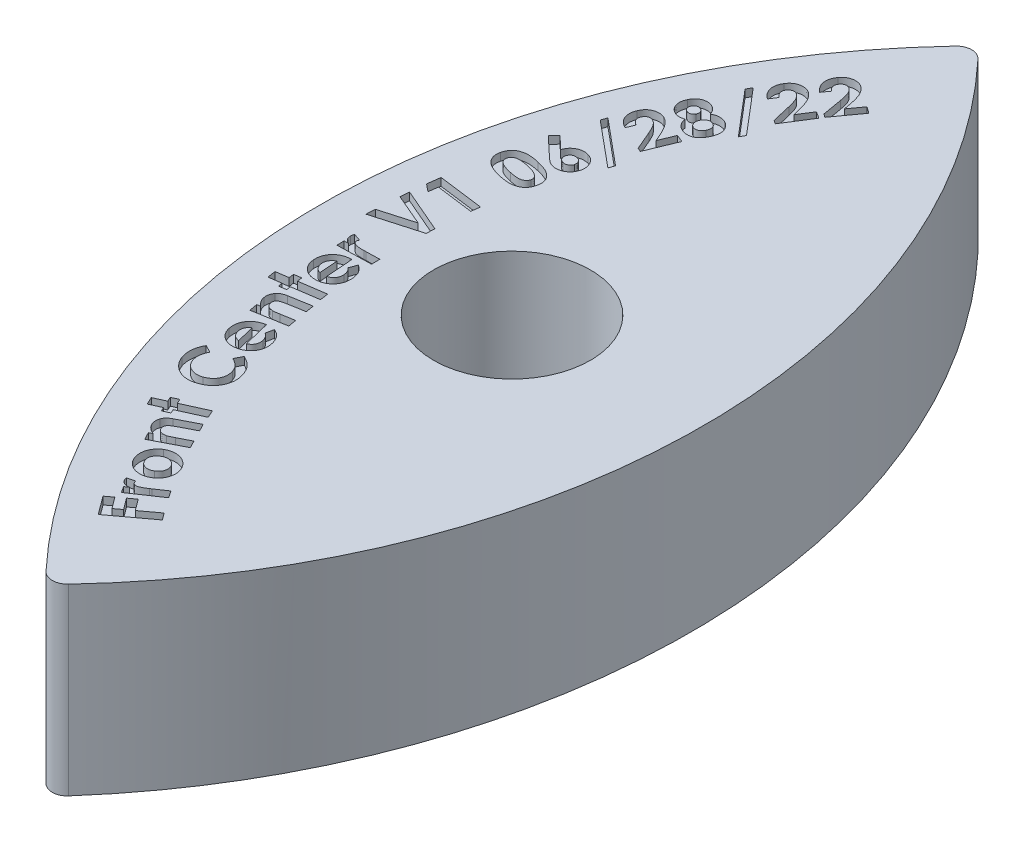
SolidWorks part; units mm, degrees
ref_plane "Front Plane" through (0, 0, 0) normal (0, 0, 1) x (1, 0, 0)
ref_plane "Top Plane" through (0, 0, 0) normal (0, 1, 0) x (1, 0, 0)
ref_plane "Right Plane" through (0, 0, 0) normal (1, 0, 0) x (0, 0, -1)
sketch "Sketch2" plane through (0, 0, 0) normal (1, 0, 0) x (0, 0, -1)
  line L0 (-15.7391, 19.787) -> (12.7788, 17.9806) construction
  line L1 (-38.1, -0.927) -> (-38.1, 14.2875)
  line L2 (-38.1, 14.2875) -> (38.1, 14.2875)
  line L3 (38.1, 14.2875) -> (38.1, 0.452)
  line L4 (-38.1, 0) -> (38.1, 0) construction
  line L5 (-302.918, -43.2315) -> (-283.9965, -45.4399) construction
  spline S0 degree 2 poles (-38.1, -0.927) (-0.0086, 0.2374) (38.1, 0.452) knots 0 0 0 1 1 1
  point P4 (0, -3.7491)
  point P8 (-38.1, -0.927)
  point P9 (0, 0)
  point P10 (38.1, 0.1903)
  point P11 (38.1, 0.452)
  dimension "D1" = 28.575
  dimension "D2" = 14.2875
  dimension "D3" = 19.05
  dimension "D4" = 76.2
extrude "Boss-Extrude1" add sketch "Sketch2" against normal mid plane 31.75
sketch "Sketch3" plane through (0, 14.2875, 0) normal (0, 1, 0) x (1, 0, 0)
  line L0 (-15.875, 38.1) -> (-15.875, -38.1) construction
  line L1 (0, 0) -> (0, 38.1) construction
  line L2 (-15.875, 38.1) -> (15.875, 38.1) construction
  line L3 (15.875, 38.1) -> (15.875, -38.1) construction
  line L4 (-15.875, -38.1) -> (15.875, -38.1) construction
  line L9 (15.875, -38.1) -> (15.875, 38.1)
  line L10 (15.875, 38.1) -> (-15.875, 38.1)
  line L11 (-15.875, 38.1) -> (-15.875, -38.1)
  line L12 (-15.875, -38.1) -> (15.875, -38.1)
  line L13 (15.875, -38.1) -> (15.875, 38.1)
  line L14 (15.875, 38.1) -> (-15.875, 38.1)
  line L15 (-15.875, 38.1) -> (-15.875, -38.1)
  line L16 (-15.875, -38.1) -> (15.875, -38.1)
  arc A0 (-0.9249, 37.7004) -> (-0.9249, -37.7004) centre (39.1353, 0) ccw
  arc A1 (0.9249, 37.7004) -> (0.9249, -37.7004) centre (-39.1353, 0) cw
  arc A2 (0.9249, 37.7004) -> (-0.9249, 37.7004) centre (0, 36.83) ccw
  arc A3 (0.9249, -37.7004) -> (-0.9249, -37.7004) centre (0, -36.83) cw
  circle A4 centre (0, 0) radius 6.5
  dimension "D1" = 1.27
  dimension "D3" = 13
  dimension "D2" = 0
extrude "Cut-Extrude1" cut sketch "Sketch3" against normal through all
sketch "Sketch5" plane through (0, 14.2875, 0) normal (0, 1, 0) x (1, 0, 0)
  arc A2 (3.6994, 33.3485) -> (3.6994, -33.3485) centre (39.1353, 0) ccw
  arc A3 (3.6138, 33.2573) -> (3.6994, -33.3485) centre (39.1353, 0) ccw
  point P3 (0, 0)
  point P4 (-8.6581, 9.144)
  point P6 (-7.8247, 12.7508)
  point P7 (3.6994, 33.2573)
  dimension "D1" = 6.35
sketch "Sketch6" plane through (0, 14.2875, 0) normal (0, 1, 0) x (1, 0, 0)
  text T0 "<b>Front Center V1 06/28/22</b>" font "Century Gothic" height 3.81
extrude "Cut-Extrude2" cut sketch "Sketch6" against normal blind 0.635
